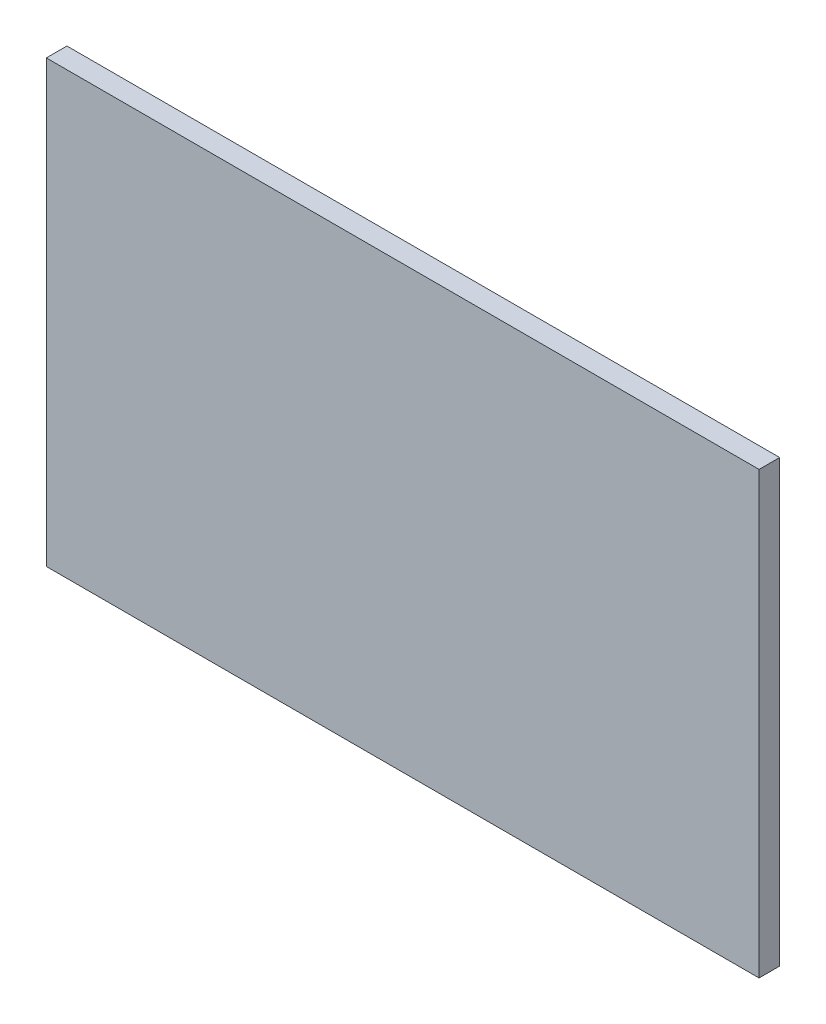
SolidWorks part; units mm, degrees
ref_plane "Front Plane" through (0, 0, 0) normal (0, 0, 1) x (1, 0, 0)
ref_plane "Top Plane" through (0, 0, 0) normal (0, 1, 0) x (1, 0, 0)
ref_plane "Right Plane" through (0, 0, 0) normal (1, 0, 0) x (0, 0, -1)
sketch "Sketch1" plane through (0, 0, 0) normal (0, 0, 1) x (1, 0, 0)
  line L1 (311.5, -192.5) -> (-311.5, -192.5)
  line L2 (311.5, -192.5) -> (311.5, 192.5)
  line L3 (311.5, 192.5) -> (-311.5, 192.5)
  line L4 (-311.5, -192.5) -> (-311.5, 192.5)
  line L5 (311.5, -192.5) -> (-311.5, 192.5) construction
  line L6 (311.5, 192.5) -> (-311.5, -192.5) construction
  point P0 (0, 0)
  dimension "D1" = 385
  dimension "D2" = 623
extrude "Boss-Extrude1" add sketch "Sketch1" along normal blind 18
equation "\"H_DSP\"=18"
equation "\"D1@Boss-Extrude1\"=\"H_DSP\""
